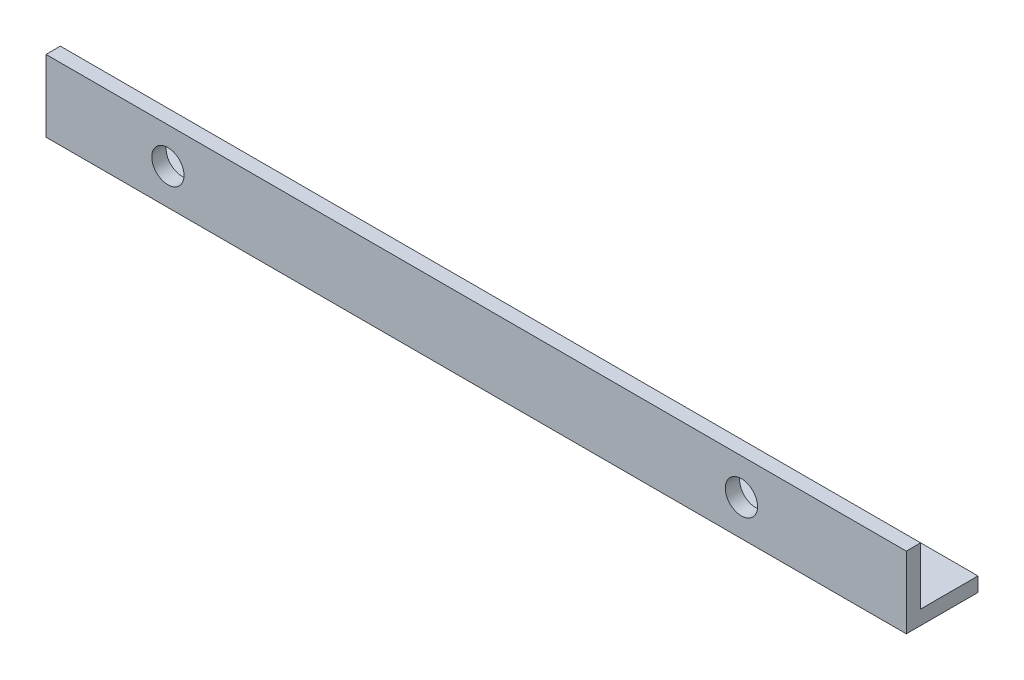
SolidWorks part; units mm, degrees
ref_plane "Спереди" through (0, 0, 0) normal (0, 0, 1) x (1, 0, 0)
ref_plane "Сверху" through (0, 0, 0) normal (0, 1, 0) x (1, 0, 0)
ref_plane "Справа" through (0, 0, 0) normal (1, 0, 0) x (0, 0, -1)
sketch "Эскиз1" plane through (0, 0, 0) normal (1, 0, 0) x (0, 0, -1)
  line L0 (0, 0) -> (0, 10)
  line L1 (0, 10) -> (2, 10)
  line L2 (2, 10) -> (2, 2)
  line L3 (2, 2) -> (10, 2)
  line L4 (10, 2) -> (10, 0)
  line L5 (10, 0) -> (0, 0)
  dimension "D1" = 2
  dimension "D2" = 2
  dimension "D3" = 10
  dimension "D4" = 10
extrude "Бобышка-Вытянуть1" add sketch "Эскиз1" along normal blind 120
sketch "Эскиз2" plane through (0, 0, 0) normal (0, 0, 1) x (1, 0, 0)
  line L1 (120, 0) -> (0, 0) construction
  line L2 (120, 10) -> (120, 0) construction
  circle A0 centre (97, 5) radius 2.25
  circle A1 centre (17, 5) radius 2.25
  dimension "D1" = 80
  dimension "D4" = 4.5
  dimension "D2" = 5
  dimension "D3" = 23
extrude "Вырез-Вытянуть1" cut sketch "Эскиз2" against normal up to next
sketch "Эскиз3" plane through (0, 0, 0) normal (0, -1, 0) x (1, 0, 0)
  line L0 (120, 0) -> (0, 0) construction
  line L1 (120, 0) -> (120, -10) construction
  circle A0 centre (103, -5) radius 2.25
  circle A1 centre (23, -5) radius 2.25
  dimension "D1" = 4.5
  dimension "D2" = 5
  dimension "D3" = 80
  dimension "D4" = 17
extrude "Вырез-Вытянуть2" cut sketch "Эскиз3" against normal up to next
